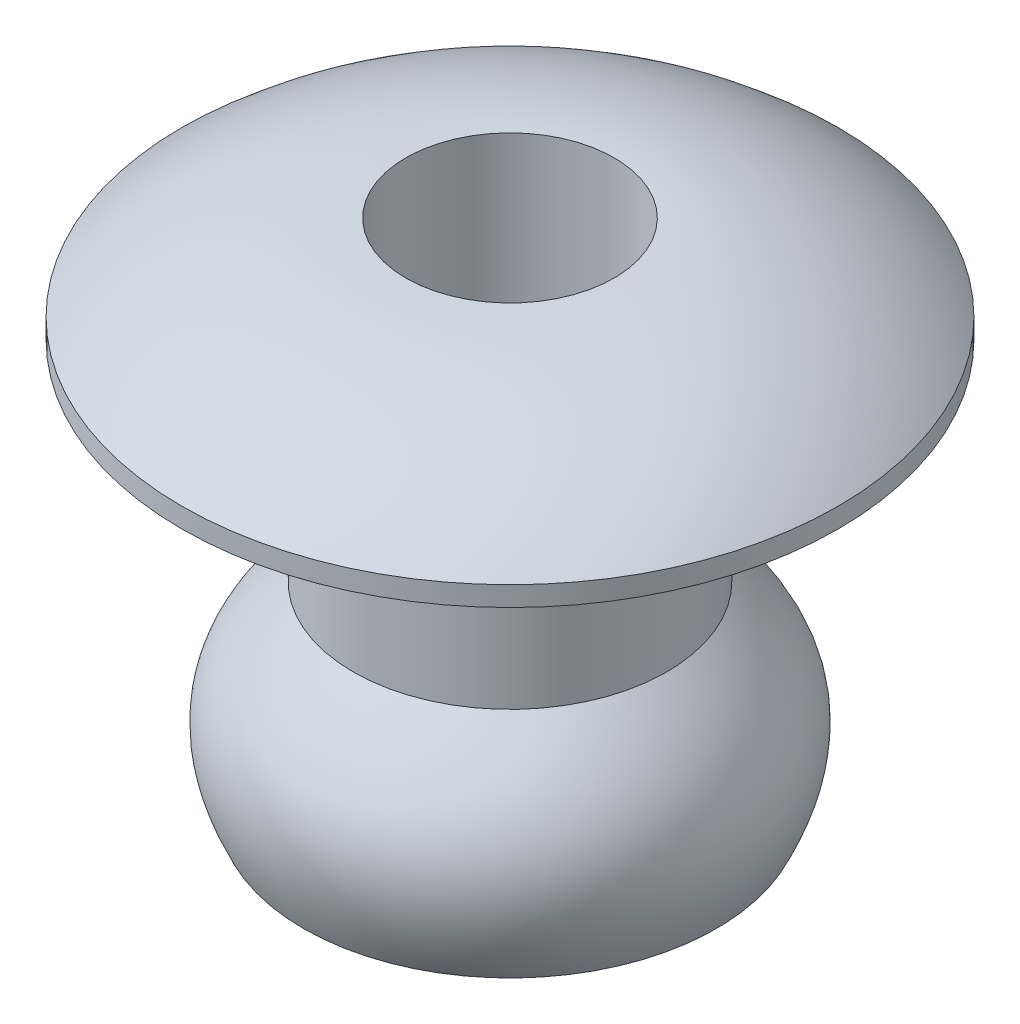
SolidWorks part; units mm, degrees
material "Alloy Steel"
ref_plane "Front Plane" through (0, 0, 0) normal (0, 0, 1) x (1, 0, 0)
ref_plane "Top Plane" through (0, 0, 0) normal (0, 1, 0) x (1, 0, 0)
ref_plane "Right Plane" through (0, 0, 0) normal (1, 0, 0) x (0, 0, -1)
sketch "Sketch1" plane through (0, 0, 0) normal (1, 0, 0) x (0, 0, -1)
  line L0 (0, 0) -> (0, -3.175) construction
  line L1 (-2.3813, 0) -> (-2.3812, -3.175)
  line L2 (-2.3813, 0) -> (-4.9784, 0)
  line L3 (-4.9784, 0) -> (-4.9784, 0.3)
  line L4 (-1.5813, 1.6002) -> (-1.5812, -3.5315)
  line L5 (-2.4013, -6.175) -> (-3.1312, -6.175)
  line L6 (-1.8464, -3.7699) -> (-1.5812, -3.5315)
  line L7 (-2.412, -5.8247) -> (-2.3114, -6.0312)
  arc A0 (-1.5813, 1.6002) -> (-4.9784, 0.3) centre (-1.5812, -3.4879) ccw
  arc A1 (-2.4013, -6.175) -> (-2.3114, -6.0312) centre (-2.4013, -6.075) ccw
  spline S0 degree 3 poles (-3.1312, -6.175) (-3.803, -4.7961) (-3.2852, -3.9878) (-2.3812, -3.175) knots 0 0 0 0 0.915818 0.915818 0.915818 0.915818
  spline S1 degree 1 poles (-2.412, -5.8247) (-1.8464, -3.7699) knots 0 0 1 1 construction
  spline S2 degree 3 poles (-2.412, -5.8247) (-2.4716, -5.7023) (-2.5839, -5.4238) (-2.6387, -5.1403) (-2.6389, -4.911) (-2.5821, -4.6528) (-2.4262, -4.3706) (-2.1393, -4.0431) (-1.9423, -3.8561) (-1.8464, -3.7699) knots 0 0 0 0 0.114477 0.228955 0.343432 0.457909 0.686864 0.801341 0.915818 0.915818 0.915818 0.915818
  point P10 (-3.4179, -4.8784)
  dimension "D12" = 0.1
  dimension "D1" = 3.175
  dimension "D2" = 0.3
  dimension "D3" = 1.6002
  dimension "D4" = 2.3813
  dimension "D5" = 4.9784
  dimension "D6" = 0.8
  dimension "D7" = 0.8
  dimension "D8" = 0.75
  dimension "D9" = 3
  dimension "D10" = 1.3
  dimension "D11" = 0.3
revolve "Revolve1" add sketch "Sketch1" angle 360 about L0
